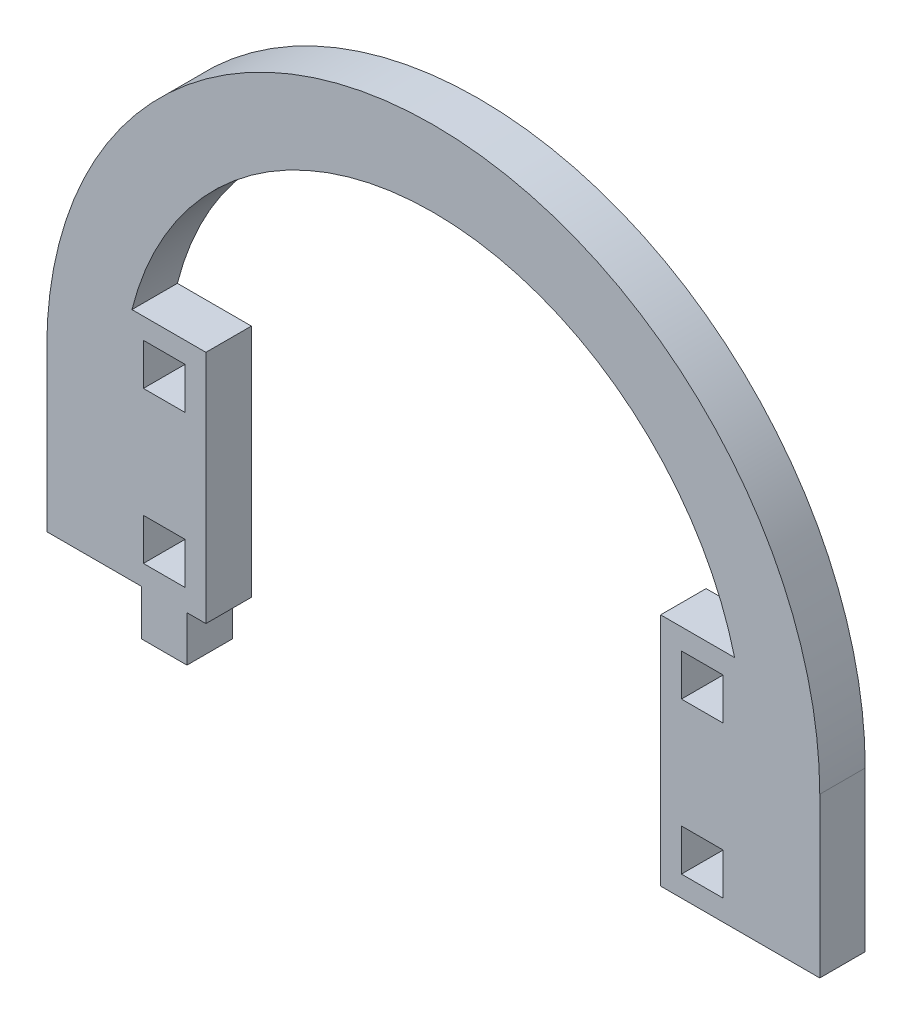
SolidWorks part; units mm, degrees
ref_plane "Front Plane" through (0, 0, 0) normal (0, 0, 1) x (1, 0, 0)
ref_plane "Top Plane" through (0, 0, 0) normal (0, 1, 0) x (1, 0, 0)
ref_plane "Right Plane" through (0, 0, 0) normal (1, 0, 0) x (0, 0, -1)
sketch "Model" plane through (0, 0, 0) normal (0, 0, 1) x (1, 0, 0)
  line L0 (3413.843, 1402.05) -> (3413.843, 1381.05)
  line L1 (3515.843, 1402.05) -> (3515.843, 1381.05)
  line L2 (3515.843, 1381.05) -> (3505.843, 1381.05)
  line L3 (3503.093, 1389.3) -> (3497.593, 1389.3)
  line L4 (3497.593, 1389.3) -> (3497.593, 1383.8)
  line L5 (3497.593, 1383.8) -> (3503.093, 1383.8)
  line L6 (3503.093, 1383.8) -> (3503.093, 1389.3)
  line L7 (3494.843, 1381.05) -> (3505.843, 1381.05)
  line L8 (3503.093, 1409.3) -> (3497.593, 1409.3)
  line L9 (3497.593, 1409.3) -> (3497.593, 1403.8)
  line L10 (3497.593, 1403.8) -> (3503.093, 1403.8)
  line L11 (3503.093, 1403.8) -> (3503.093, 1409.3)
  line L12 (3504.6048, 1412.05) -> (3494.843, 1412.05)
  line L13 (3432.093, 1389.3) -> (3426.593, 1389.3)
  line L14 (3426.593, 1389.3) -> (3426.593, 1383.8)
  line L15 (3426.593, 1383.8) -> (3432.093, 1383.8)
  line L16 (3432.093, 1383.8) -> (3432.093, 1389.3)
  line L17 (3432.343, 1381.05) -> (3434.843, 1381.05)
  line L18 (3426.343, 1381.05) -> (3426.343, 1375.05)
  line L19 (3426.343, 1375.05) -> (3432.343, 1375.05)
  line L20 (3432.343, 1375.05) -> (3432.343, 1381.05)
  line L21 (3432.093, 1409.3) -> (3426.593, 1409.3)
  line L22 (3426.593, 1409.3) -> (3426.593, 1403.8)
  line L23 (3426.593, 1403.8) -> (3432.093, 1403.8)
  line L24 (3432.093, 1403.8) -> (3432.093, 1409.3)
  line L25 (3434.843, 1412.05) -> (3425.0812, 1412.05)
  line L26 (3434.843, 1412.05) -> (3434.843, 1381.05)
  line L27 (3494.843, 1412.05) -> (3494.843, 1381.05)
  line L28 (3413.843, 1381.05) -> (3426.343, 1381.05)
  arc A0 (3515.843, 1402.05) -> (3413.843, 1402.05) centre (3464.843, 1402.05) ccw
  arc A1 (3504.6048, 1412.05) -> (3425.0812, 1412.05) centre (3464.843, 1402.05) ccw
extrude "Boss-Extrude1" add sketch "Model" along normal blind 6 contours L23 L24 L21 L22 | L5 L6 L3 L4 | L0 L28 L18 L19 L20 L17 L26 L25 A1 L12 L27 L7 L2 L1 A0 | L13 L14 L15 L16 | L11 L8 L9 L10
